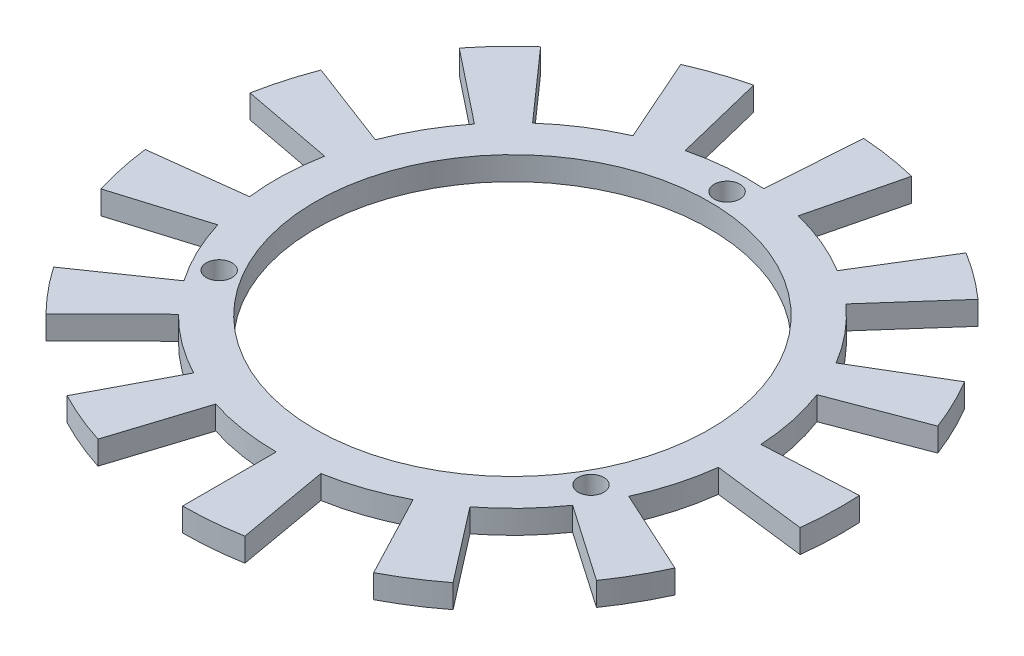
SolidWorks part; units mm, degrees
material "AISI 1010 Steel, hot rolled bar"
ref_plane "Front Plane" through (0, 0, 0) normal (0, 0, 1) x (1, 0, 0)
ref_plane "Top Plane" through (0, 0, 0) normal (0, 1, 0) x (1, 0, 0)
ref_plane "Right Plane" through (0, 0, 0) normal (1, 0, 0) x (0, 0, -1)
sketch "Sketch1" plane through (0, 0, 0) normal (0, 1, 0) x (1, 0, 0)
  circle A0 centre (0, 0) radius 25.25
  dimension "D1" = 50.5
extrude "Extrude-Thin1" add sketch "Sketch1" against normal blind 3 thin
sketch "Sketch2" plane through (0, 0, 0) normal (0, 1, 0) x (1, 0, 0)
  line L0 (0, -30.25) -> (0, 30.25) construction
  line L1 (0, 0) -> (23.8157, -13.75) construction
  line L2 (0, 0) -> (-23.8157, -13.75) construction
  circle A0 centre (0, 27.5) radius 1.65
  circle A1 centre (0, 0) radius 30.25 construction
  circle A4 centre (0, 0) radius 27.5 construction
  circle A7 centre (23.8157, -13.75) radius 1.65
  circle A8 centre (-23.8157, -13.75) radius 1.65
  dimension "D1" = 55
  dimension "D2" = 3.3
  dimension "D3" = 120
  dimension "D4" = 120
extrude "Cut-Extrude3" cut sketch "Sketch2" against normal blind 10
sketch "Sketch5" plane through (0, -3, 0) normal (0, -1, 0) x (1, 0, 0)
  line L0 (0, 0) -> (0, 35.9971) construction
  line L1 (0, 0) -> (5.9226, 33.5886) construction
  line L2 (0, 42.25) -> (0, 30.25)
  line L3 (5.2529, 29.7904) -> (7.3366, 41.6081)
  line L4 (19.6346, 37.4105) -> (14.0579, 26.785)
  line L5 (18.4955, 23.937) -> (25.8325, 33.4327)
  line L6 (34.7711, 24.0007) -> (24.8953, 17.184)
  line L7 (27.501, 12.5999) -> (38.4105, 17.5982)
  line L8 (41.9419, 5.0927) -> (30.0294, 3.6462)
  line L9 (30.2064, -1.6237) -> (42.1891, -2.2678)
  line L10 (39.5044, -14.9821) -> (28.2842, -10.7268)
  line L11 (25.9919, -15.4753) -> (36.3027, -21.6143)
  line L12 (28.0169, -31.6246) -> (20.0595, -22.6425)
  line L13 (15.8229, -25.7817) -> (22.0997, -36.0092)
  line L14 (10.1111, -41.0223) -> (7.2393, -29.371)
  line L15 (2.0291, -30.1819) -> (2.834, -42.1548)
  line L16 (-10.1111, -41.0223) -> (-7.2393, -29.371)
  line L17 (-12.2295, -27.6677) -> (-17.0809, -38.6433)
  line L18 (-28.0169, -31.6246) -> (-20.0595, -22.6425)
  line L19 (-23.6865, -18.8152) -> (-33.0828, -26.279)
  line L20 (-39.5044, -14.9821) -> (-28.2842, -10.7268)
  line L21 (-29.7172, -5.6523) -> (-41.5059, -7.8946)
  line L48 (-41.9419, 5.0927) -> (-30.0294, 3.6462)
  line L49 (-28.9401, 8.8054) -> (-40.4204, 12.2984)
  line L50 (-34.7711, 24.0007) -> (-24.8953, 17.184)
  line L51 (-21.5331, 21.2459) -> (-30.0751, 29.674)
  line L52 (-19.6346, 37.4105) -> (-14.0579, 26.785)
  line L53 (-9.1931, 28.8192) -> (-12.84, 40.2517)
  circle A0 centre (0, 0) radius 30.25 construction
  arc A1 (5.2529, 29.7904) -> (0, 30.25) centre (0, 0) ccw
  arc A2 (7.3366, 41.6081) -> (0, 42.25) centre (0, 0) ccw
  arc A3 (25.8325, 33.4327) -> (19.6346, 37.4105) centre (0, 0) ccw
  arc A4 (18.4955, 23.937) -> (14.0579, 26.785) centre (0, 0) ccw
  arc A5 (38.4105, 17.5982) -> (34.7711, 24.0007) centre (0, 0) ccw
  arc A6 (27.501, 12.5999) -> (24.8953, 17.184) centre (0, 0) ccw
  arc A7 (42.1891, -2.2678) -> (41.9419, 5.0927) centre (0, 0) ccw
  arc A8 (30.2064, -1.6237) -> (30.0294, 3.6462) centre (0, 0) ccw
  arc A9 (36.3027, -21.6143) -> (39.5044, -14.9821) centre (0, 0) ccw
  arc A10 (25.9919, -15.4753) -> (28.2842, -10.7268) centre (0, 0) ccw
  arc A11 (22.0997, -36.0092) -> (28.0169, -31.6246) centre (0, 0) ccw
  arc A12 (15.8229, -25.7817) -> (20.0595, -22.6425) centre (0, 0) ccw
  arc A13 (2.834, -42.1548) -> (10.1111, -41.0223) centre (0, 0) ccw
  arc A14 (2.0291, -30.1819) -> (7.2393, -29.371) centre (0, 0) ccw
  arc A15 (-17.0809, -38.6433) -> (-10.1111, -41.0223) centre (0, 0) ccw
  arc A16 (-12.2295, -27.6677) -> (-7.2393, -29.371) centre (0, 0) ccw
  arc A17 (-33.0828, -26.279) -> (-28.0169, -31.6246) centre (0, 0) ccw
  arc A18 (-23.6865, -18.8152) -> (-20.0595, -22.6425) centre (0, 0) ccw
  arc A19 (-41.5059, -7.8946) -> (-39.5044, -14.9821) centre (0, 0) ccw
  arc A20 (-29.7172, -5.6523) -> (-28.2842, -10.7268) centre (0, 0) ccw
  arc A47 (-40.4204, 12.2984) -> (-41.9419, 5.0927) centre (0, 0) ccw
  arc A48 (-28.9401, 8.8054) -> (-30.0294, 3.6462) centre (0, 0) ccw
  arc A49 (-30.0751, 29.674) -> (-34.7711, 24.0007) centre (0, 0) ccw
  arc A50 (-21.5331, 21.2459) -> (-24.8953, 17.184) centre (0, 0) ccw
  arc A51 (-12.84, 40.2517) -> (-19.6346, 37.4105) centre (0, 0) ccw
  arc A52 (-9.1931, 28.8192) -> (-14.0579, 26.785) centre (0, 0) ccw
  point P87 (0, 0)
  dimension "D2" = 12
  dimension "D1" = 10
  dimension "D3" = 13
extrude "Boss-Extrude1" add sketch "Sketch5" against normal blind 3
